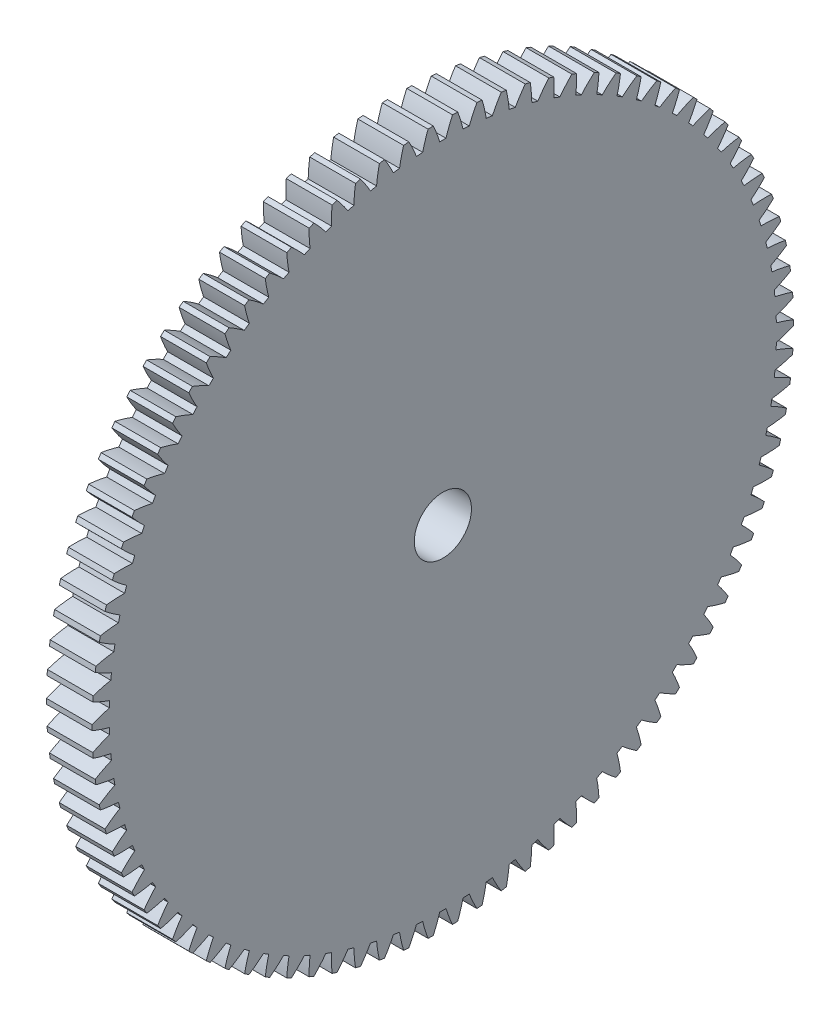
SolidWorks part; units mm, degrees
ref_plane "Plane1" through (0, 0, 0) normal (0, 0, 1) x (1, 0, 0)
ref_plane "Plane2" through (0, 0, 0) normal (0, 1, 0) x (1, 0, 0)
ref_plane "Plane3" through (0, 0, 0) normal (1, 0, 0) x (0, 0, -1)
other "Configuration Table"
sketch "HoldingSke" plane through (0, 0, 0) normal (0, 1, 0) x (1, 0, 0)
  line L0 (0, 0) -> (0, -0.5)
  line L1 (-15, 0) -> (100, 0) construction
  line L2 (0, 0) -> (-2.1039, 2.3779)
  line L3 (0, 0) -> (-11.863, 4.5341)
  line L4 (0, 0) -> (0, 8.636)
  line L5 (0, 0) -> (-46.8476, -17.4728)
  line L6 (0, 0) -> (-9.9476, -6.7116)
  line L7 (-2.1039, 2.3779) -> (8.6586, 51.2059)
  line L8 (-76.2, 54.61) -> (-73.9, 54.61)
  line L9 (-71.009, 38.7566) -> (-53.1078, 45.2721)
  line L10 (-76.2, 71.12) -> (104.1128, 71.12)
  line L11 (0, 0) -> (-12, 0)
  line L12 (-76.2, 101.6) -> (-76.133, 101.6)
  line L13 (24.9733, 27.94) -> (52.9518, 28.4284)
  line L14 (24.9733, 27.94) -> (24.9743, 27.94)
  line L15 (24.9733, 27.94) -> (100.4006, 29.5858)
  line L16 (-63.627, -2) -> (-12.827, -2)
  circle A0 centre (0, 0) radius 7.5
  circle A1 centre (0, 0) radius 37.5
  circle A2 centre (0, 0) radius 37.5
  circle A3 centre (0, 0) radius 7.5
  dimension "MHD" = 75
  dimension "Hub_dia" = 75
  dimension "Bore" = 15
  dimension "MBD" = 15
  dimension "Num_teeth" = 90
  dimension "Pitch" = 0.5
  dimension "Overall_len" = 50
  dimension "Show_teeth" = 90
  dimension "Thickness" = 12
  dimension "OAL" = 50.0001
  dimension "T_dim" = 2.3
  dimension "Ap" = 20
  dimension "H" = 19.05
  dimension "Pitch_radius" = 180.3128
  dimension "Width" = 12
  dimension "Backlash" = 0.067
  dimension "Addendum_fac" = 1
  dimension "Dedendum_fac" = 1.25
  dimension "Clearance_fac" = 0.25
  dimension "Dedendum_add" = 0.001
  dimension "Module" = 2
sketch "BasProSke" plane through (0, 0, 0) normal (0, 1, 0) x (1, 0, 0)
  line L0 (-10, 0) -> (60, 0) construction
  line L1 (0, 0) -> (0, 92)
  line L2 (0, 0) -> (12, 0)
  line L3 (12, 0) -> (12, 92)
  line L4 (12, 92) -> (0, 92)
  dimension "Thickness" = 12
  dimension "Diameter" = 184
revolve "Base-Revolve" add sketch "BasProSke" angle 360 about L0
sketch "TooCutSke" plane through (0, 0, 0) normal (1, 0, 0) x (0, 0, -1)
  line L1 (0, 0) -> (0, 107) construction
  line L2 (0, 0) -> (-1.688, 89.9842) construction
  line L3 (0, 0) -> (-6.2811, 179.8669) construction
  line L4 (-1.688, 89.9842) -> (-3.1405, 89.9334) construction
  arc A0 (0.8196, 87.4952) -> (-0.8196, 87.4952) centre (0, 0) ccw
  arc A1 (2.5423, 91.9903) -> (-2.5423, 91.9903) centre (0, 0) ccw
  circle A2 centre (0, 0) radius 90 construction
  circle A3 centre (0, 0) radius 84.5723 construction
  arc A4 (-0.8196, 87.4952) -> (-2.5423, 91.9903) centre (-35.2218, 76.8889) ccw
  arc A5 (2.5423, 91.9903) -> (0.8196, 87.4952) centre (35.2218, 76.8889) ccw
  dimension "Root_dia" = 174.998
  dimension "Overcut_dia" = 184.0508
  dimension "Pitch_dia" = 180
  dimension "Base_dia" = 169.1447
  dimension "Flank_rad" = 36
  dimension "Half_ang" = 2
  dimension "Half_CT" = 1.4535
extrude "ToothCut" cut sketch "TooCutSke" along normal through all
fillet "Breaks" [suppressed] radius 0.04
fillet "RootFillets" [suppressed] radius 0.501
pattern_circular "TeethCuts" count 90 every 4 about axis through (-10, 0, 0) along (1, 0, 0) of "ToothCut", "RootFillets", "Breaks"
sketch "HubNeaOneSke" plane through (0, 0, 0) normal (-1, 0, 0) x (0, 0, 1)
  circle A0 centre (0, 0) radius 37.5
  dimension "Diameter" = 75
extrude "HubNearOne" [suppressed] add sketch "HubNeaOneSke" along normal blind 38.0001
sketch "HubNeaBotSke" plane through (0, 0, 0) normal (-1, 0, 0) x (0, 0, 1)
  circle A0 centre (0, 0) radius 37.5
  dimension "Diameter" = 75
extrude "HubNearBoth" [suppressed] add sketch "HubNeaBotSke" along normal blind 19
ref_plane "FarPln" through (12, 0, 0) normal (1, 0, 0) x (0, 0, -1)
sketch "HubFarSke" plane through (12, 0, 0) normal (1, 0, 0) x (0, 0, -1)
  circle A0 centre (0, 0) radius 37.5
  dimension "Diameter" = 75
extrude "HubFar" [suppressed] add sketch "HubFarSke" along normal blind 19
sketch "BorSke" plane through (0, 0, 0) normal (1, 0, 0) x (0, 0, -1)
  circle A0 centre (0, 0) radius 7.5
  dimension "Diameter" = 15
extrude "Bore" cut sketch "BorSke" along normal mid plane 100.0001
sketch "KeySke" plane through (0, 0, 0) normal (1, 0, 0) x (0, 0, -1)
  line L0 (-2.5, 0) -> (-2.5, 9.8)
  line L1 (-2.5, 9.8) -> (2.5, 9.8)
  line L2 (2.5, 9.8) -> (2.5, 0)
  line L3 (0, 0) -> (0, 34) construction
  line L4 (-2.5, 0) -> (2.5, 0)
  dimension "Offset" = 9.8
  dimension "Width" = 5
extrude "Keyway" [suppressed] cut sketch "KeySke" along normal mid plane 100.0001
pattern_circular "Keyway2" [suppressed] count 2 every 90 about axis through (-10, 0, 0) along (1, 0, 0)
equation "' \"Module@HoldingSke\" = 6.35"
equation "' \"Num_teeth@HoldingSke\" = 12"
equation "' \"Ap@HoldingSke\" =  20"
equation "' \"Ap@HoldingSke\" = 20"
equation "' \"Width@HoldingSke\" = 0.5 * 25.4"
equation "' \"Hub_dia@HoldingSke\"= 1 * 25.4"
equation "' \"Hub_dia@HoldingSke\" = 1 * 25.4"
equation "' \"Overall_len@HoldingSke\" = 1.0 * 25.4"
equation "' \"Bore@HoldingSke\" = 0.75 * 25.4"
equation "' \"T_dim@HoldingSke\" = 0.1 * 25.4"
equation "' \"Width@KeySke\" = 0.25 * 25.4"
equation "' \"Show_teeth@HoldingSke\" = 13"
equation "' \"Backlash@HoldingSke\" = 0.009 * 25.4"
equation "' \"Addendum_fac@HoldingSke\" = 1.0"
equation "' \"Dedendum_fac@HoldingSke\" = 1.25"
equation "' \"Dedendum_add@HoldingSke\" = 0.00005 * 25.4"
equation "' \"Clearance_fac@HoldingSke\" = 0.25"
equation "\"Pitch@HoldingSke\" = 1 / \"Module@HoldingSke\""
equation "\"Overcut_dia@TooCutSke\" = (\"Num_teeth@HoldingSke\" + 2 * \"Addendum_fac@HoldingSke\") / \"Pitch@HoldingSke\" + 0.002 * 25.4"
equation "\"Pitch_dia@TooCutSke\" = \"Num_teeth@HoldingSke\" / \"Pitch@HoldingSke\""
equation "\"Base_dia@TooCutSke\" = \"Num_teeth@HoldingSke\" / \"Pitch@HoldingSke\" * cos((\"Ap@HoldingSke\"  * 3.14159265 / 180))"
equation "\"Root_dia@TooCutSke\" = (\"Num_teeth@HoldingSke\" + 2) / \"Pitch@HoldingSke\" - 2 * (\"Addendum_fac@HoldingSke\" + \"Dedendum_fac@HoldingSke\") / \"Pitch@HoldingSke\" - \"Dedendum_add@HoldingSke\" * 2"
equation "\"Half_ang@TooCutSke\" = 180 / \"Num_teeth@HoldingSke\""
equation "\"Half_CT@TooCutSke\" = \"Num_teeth@HoldingSke\" / \"Pitch@HoldingSke\" * sin((3.14159265 / 2 / \"Num_teeth@HoldingSke\")) / 2 - 7 * \"Backlash@HoldingSke\" / 4"
equation "\"Flank_rad@TooCutSke\" = \"Num_teeth@HoldingSke\" / \"Pitch@HoldingSke\" / 5"
equation "\"Radius@RootFillets\" = \"Clearance_fac@HoldingSke\" / \"Pitch@HoldingSke\" + \"Dedendum_add@HoldingSke\""
equation "\"Break_rad@Breaks\" = 0.02 / \"Pitch@HoldingSke\""
equation "\"Thickness@HoldingSke\" = \"Width@HoldingSke\""
equation "\"OAL@HoldingSke\" = \"Thickness@HoldingSke\""
equation "\"MHD@HoldingSke\" = (\"Num_teeth@HoldingSke\" + 2) / \"Pitch@HoldingSke\" - 2 * (\"Addendum_fac@HoldingSke\" + \"Dedendum_fac@HoldingSke\")  / \"Pitch@HoldingSke\" - \"Dedendum_add@HoldingSke\" * 2"
equation "\"MBD@HoldingSke\" = (\"Num_teeth@HoldingSke\" + 2) / \"Pitch@HoldingSke\" - 2 * (\"Addendum_fac@HoldingSke\" + \"Dedendum_fac@HoldingSke\")  / \"Pitch@HoldingSke\" - \"Dedendum_add@HoldingSke\" * 2 - 0.002 * 25.4"
equation "\"MHD@HoldingSke\" = ((sgn( \"MHD@HoldingSke\" - \"Hub_dia@HoldingSke\" )-1)*( \"MHD@HoldingSke\" - \"Hub_dia@HoldingSke\" ))/-2+ \"Hub_dia@HoldingSke\""
equation "\"MBD@HoldingSke\" = ((sgn( \"MBD@HoldingSke\" - \"Bore@HoldingSke\" )-1)*( \"MBD@HoldingSke\" - \"Bore@HoldingSke\" ))/-2+ \"Bore@HoldingSke\""
equation "\"OAL@HoldingSke\" = ((sgn( \"OAL@HoldingSke\" - \"Overall_len@HoldingSke\" )+1)*( \"OAL@HoldingSke\" - \"Overall_len@HoldingSke\" ))/2 + \"Overall_len@HoldingSke\" + 0.000002 * 25.4"
equation "\"Num_teeth@TeethCuts\" = int( \"Show_teeth@HoldingSke\" ) + 1"
equation "\"Num_teeth@TeethCuts\" = ((sgn( \"Num_teeth@TeethCuts\" - \"Num_teeth@HoldingSke\" )-1)*( \"Num_teeth@TeethCuts\" - \"Num_teeth@HoldingSke\" ))/-2+ \"Num_teeth@HoldingSke\""
equation "\"Num_teeth@TeethCuts\" = ((sgn( \"Num_teeth@TeethCuts\" - 2.0)+1)*( \"Num_teeth@TeethCuts\" - 2.0))/2 +2.0"
equation "\"Angle@TeethCuts\" = 360.0 / \"Num_teeth@HoldingSke\""
equation "\"Diameter@BasProSke\" = (\"Num_teeth@HoldingSke\" + 2 * \"Addendum_fac@HoldingSke\") / \"Pitch@HoldingSke\""
equation "\"Thickness@BasProSke\"  = \"Thickness@HoldingSke\""
equation "' \"Fillet_rad@BasProSke\" =  \"Thickness@HoldingSke\" * 0.05"
equation "' \"Fillet_rad@BasProSke\" = \"Thickness@HoldingSke\" * 0.05"
equation "\"MHD@HoldingSke\" = ((sgn( \"MHD@HoldingSke\" - \"Root_dia@TooCutSke\" )-1)*( \"MHD@HoldingSke\" - \"Root_dia@TooCutSke\" ))/-2+ \"Root_dia@TooCutSke\""
equation "\"Diameter@HubNeaOneSke\" = \"MHD@HoldingSke\""
equation "\"Length@HubNearOne\" = \"OAL@HoldingSke\" - \"Thickness@BasProSke\""
equation "\"Diameter@HubNeaBotSke\" = \"MHD@HoldingSke\""
equation "\"Length@HubNearBoth\" = ( \"OAL@HoldingSke\" - \"Thickness@BasProSke\" ) / 2.0"
equation "\"Thickness@FarPln\" = \"Thickness@BasProSke\""
equation "\"Diameter@HubFarSke\" = \"MHD@HoldingSke\""
equation "\"Length@HubFar\" = ( \"OAL@HoldingSke\" - \"Thickness@BasProSke\" ) / 2.0"
equation "\"Diameter@BorSke\" = \"MBD@HoldingSke\""
equation "\"D1@Bore\" = \"OAL@HoldingSke\" * 2.0"
equation "\"D1@Keyway\" = \"OAL@HoldingSke\" * 2.0"
equation "\"Offset@KeySke\" = \"T_dim@HoldingSke\" + \"MBD@HoldingSke\" / 2.0"
